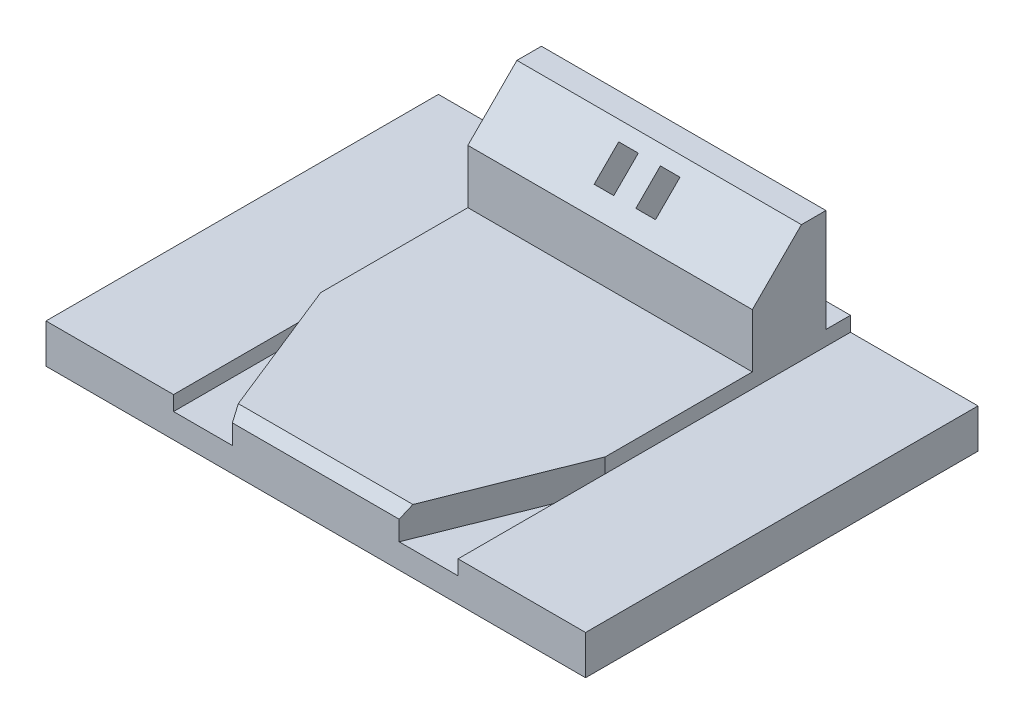
SolidWorks part; units mm, degrees
ref_plane "Front" through (0, 0, 0) normal (0, 0, 1) x (1, 0, 0)
ref_plane "Top" through (0, 0, 0) normal (0, 1, 0) x (1, 0, 0)
ref_plane "Right" through (0, 0, 0) normal (1, 0, 0) x (0, 0, -1)
sketch "草图1" plane through (0, 0, 0) normal (0, 1, 0) x (1, 0, 0)
  line L1 (55, -40) -> (-55, -40)
  line L2 (55, -40) -> (55, 40)
  line L3 (55, 40) -> (-55, 40)
  line L4 (-55, -40) -> (-55, 40)
  line L5 (55, -40) -> (-55, 40) construction
  line L6 (55, 40) -> (-55, -40) construction
  point P0 (0, 0)
  dimension "D1" = 110
  dimension "D2" = 80
extrude "凸台-拉伸1" add sketch "草图1" along normal blind 8
sketch "草图3" plane through (0, 2, 0) normal (0, 1, 0) x (1, 0, 0)
  line L0 (0, 59.7228) -> (0, -57.6598) construction
  line L2 (29, -40) -> (-29, -40)
  line L3 (29, -40) -> (29, 40)
  line L4 (29, 40) -> (-29, 40)
  line L5 (-29, -40) -> (-29, 40)
  line L6 (29, -40) -> (-29, 40) construction
  line L7 (29, 40) -> (-29, -40) construction
  line L10 (-55, -40) -> (55, -40) construction
  line L11 (55, 40) -> (-55, 40) construction
  point P3 (0, 0)
  dimension "D1" = 58
extrude "凸台-拉伸2" add sketch "草图3" along normal blind 9
sketch "草图4" plane through (0, 11, 0) normal (0, 1, 0) x (1, 0, 0)
  line L0 (0, 50.0533) -> (0, -56.1068) construction
  line L1 (-29, -10) -> (-29, -40)
  line L2 (-29, 35) -> (-29, -40) construction
  line L3 (-29, -40) -> (-17, -40)
  line L4 (-29, -40) -> (29, -40) construction
  line L5 (-17, -40) -> (-29, -10)
  line L6 (-29, 40) -> (-29, -40) construction
  line L7 (17, -40) -> (29, -10)
  line L8 (29, -40) -> (17, -40)
  line L9 (29, -10) -> (29, -40)
  dimension "D1" = 12
  dimension "D2" = 30
extrude "切除-拉伸2" cut sketch "草图4" against normal blind 6
chamfer "倒角5" distance 2 angle 45 1 edges at (0, 11, 40)
ref_plane "基准面1" through (0, 0, 0) normal (1, 0, 0) x (0, 0, -1)
sketch "草图10" plane through (0, 2, 0) normal (0, 1, 0) x (1, 0, 0)
  line L0 (0, -55) -> (0, 55) construction
  line L1 (29, 20) -> (-29, 20)
  line L2 (29, 20) -> (29, 35)
  line L3 (29, 35) -> (-29, 35)
  line L4 (-29, 20) -> (-29, 35)
  line L5 (29, 20) -> (-29, 35) construction
  line L6 (29, 35) -> (-29, 20) construction
  line L8 (-29, 40) -> (-29, -10) construction
  point P0 (0, 27.5)
  point P11 (0, 0)
  dimension "D2" = 15
extrude "凸台-拉伸5" add sketch "草图10" along normal blind 30
chamfer "倒角9" distance 10 angle 45 1 edges at (0, 32, -20)
sketch "草图11" plane through (0, 0, 0) normal (0, -1, 0) x (1, 0, 0)
  line L0 (0, -55) -> (0, 55) construction
  line L1 (-6.25, -23) -> (-2.25, -23)
  line L2 (-6.25, -23) -> (-6.25, -35)
  line L3 (-6.25, -35) -> (-2.25, -35)
  line L4 (-2.25, -23) -> (-2.25, -35)
  line L5 (-6.25, -23) -> (-2.25, -35) construction
  line L6 (-6.25, -35) -> (-2.25, -23) construction
  line L7 (6.25, -35) -> (2.25, -23) construction
  line L8 (6.25, -23) -> (2.25, -35) construction
  line L9 (2.25, -23) -> (2.25, -35)
  line L10 (6.25, -35) -> (2.25, -35)
  line L11 (6.25, -23) -> (6.25, -35)
  line L12 (6.25, -23) -> (2.25, -23)
  line L14 (55, -40) -> (-55, -40) construction
  point P0 (-4.25, -29)
  point P11 (4.25, -29)
  point P12 (-4.25, -35)
  dimension "D1" = 4
  dimension "D2" = 12
  dimension "D3" = 8.5
  dimension "D4" = 5
extrude "切除-拉伸6" cut sketch "草图11" against normal offset from surface (30 mm away) 2 up to face at (0, 32, -32.5)
sketch "草图12" plane through (0, 0, 0) normal (0, -1, 0) x (1, 0, 0)
  line L0 (-6.25, -35) -> (-2.25, -35) construction
  line L2 (0, -55) -> (0, 55) construction
  line L3 (12.5, -35) -> (-12.5, -35)
  line L4 (12.5, -35) -> (12.5, -10)
  line L5 (12.5, -10) -> (-12.5, -10)
  line L6 (-12.5, -35) -> (-12.5, -10)
  line L7 (12.5, -35) -> (-12.5, -10) construction
  line L8 (12.5, -10) -> (-12.5, -35) construction
  point P4 (0, -22.5)
  dimension "D1" = 25
  dimension "D2" = 25
extrude "切除-拉伸7" cut sketch "草图12" against normal blind 9
sketch "草图13" plane through (0, 9, 0) normal (0, -1, 0) x (1, 0, 0)
  line L0 (0, -55) -> (0, 55) construction
  line L1 (6, -18) -> (-6, -18)
  line L2 (6, -18) -> (6, -21)
  line L3 (6, -21) -> (-6, -21)
  line L4 (-6, -18) -> (-6, -21)
  line L5 (6, -18) -> (-6, -21) construction
  line L6 (6, -21) -> (-6, -18) construction
  line L7 (-6.25, -23) -> (-2.25, -23) construction
  point P0 (0, -19.5)
  dimension "D1" = 12
  dimension "D2" = 3
  dimension "D3" = 2
extrude "凸台-拉伸6" add sketch "草图13" along normal blind 5
sketch "草图14" plane through (0, 9, 0) normal (0, -1, 0) x (1, 0, 0)
  line L0 (12.5, -35) -> (12.5, -10) construction
  line L1 (-12.5, -10) -> (12.5, -10)
  line L2 (-12.5, -10) -> (-12.5, -15.96)
  line L3 (-12.5, -15.96) -> (12.5, -15.96)
  line L4 (12.5, -10) -> (12.5, -15.96)
extrude "凸台-拉伸7" add sketch "草图14" along normal blind 1
